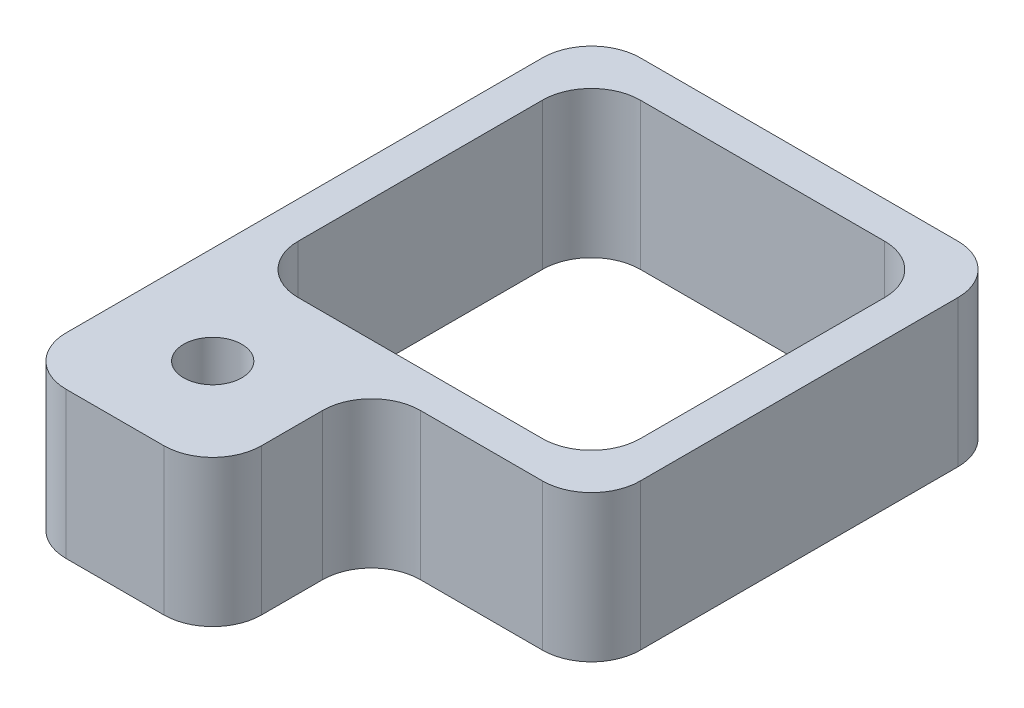
SolidWorks part; units mm, degrees
ref_plane "Front Plane" through (0, 0, 0) normal (0, 0, 1) x (1, 0, 0)
ref_plane "Top Plane" through (0, 0, 0) normal (0, 1, 0) x (1, 0, 0)
ref_plane "Right Plane" through (0, 0, 0) normal (1, 0, 0) x (0, 0, -1)
sketch "Sketch1" plane through (0, 0, 0) normal (0, 1, 0) x (1, 0, 0)
  line L1 (-4.25, -4.25) -> (4.25, -4.25)
  line L2 (-4.25, -4.25) -> (-4.25, 4.25)
  line L3 (-4.25, 4.25) -> (4.25, 4.25)
  line L4 (4.25, -4.25) -> (4.25, 4.25)
  line L5 (-4.25, -4.25) -> (4.25, 4.25) construction
  line L6 (-4.25, 4.25) -> (4.25, -4.25) construction
  point P0 (0, 0)
  dimension "D1" = 8.5
  dimension "D2" = 8.5
extrude "Extrude1" add sketch "Sketch1" along normal blind 3
sketch "Sketch3" plane through (0, 0, 4.25) normal (0, 0, 1) x (1, 0, 0)
  line L0 (-4.25, 0) -> (4.25, 0) construction
  line L1 (-4.25, 3) -> (-0.25, 3)
  line L2 (-4.25, 3) -> (-4.25, 0)
  line L3 (-4.25, 0) -> (-0.25, 0)
  line L4 (-0.25, 3) -> (-0.25, 0)
  dimension "D1" = 4
extrude "Extrude3" add sketch "Sketch3" along normal blind 3.25
sketch "Sketch2" plane through (0, 3, 0) normal (0, 1, 0) x (1, 0, 0)
  line L1 (-3.5, -3.5) -> (3.5, -3.5)
  line L2 (-3.5, -3.5) -> (-3.5, 3.5)
  line L3 (-3.5, 3.5) -> (3.5, 3.5)
  line L4 (3.5, -3.5) -> (3.5, 3.5)
  line L5 (-3.5, -3.5) -> (3.5, 3.5) construction
  line L6 (-3.5, 3.5) -> (3.5, -3.5) construction
  point P0 (0, 0)
  dimension "D1" = 7
  dimension "D2" = 7
extrude "Extrude2" cut sketch "Sketch2" against normal through all
hole_wizard "#0-80 Tapped Hole1" positions "3DSketch2" profile "Sketch6" tap size "#0-80" standard "Ansi Inch" end condition through all
sketch3d "3DSketch2"
  line L0 (-0.25, 3, 7.5) -> (-4.25, 3, 7.5) construction
  line L1 (-0.25, 3, 7.5) -> (-0.25, 3, 4.25) construction
  point P0 (-2.25, 3, 5.5)
  dimension "D1" = 2
  dimension "D2" = 2
sketch "Sketch6" plane through (-2.25, 3, 5.5) normal (1, 0, 0) x (0, 0, 1)
  line L0 (0, 0) -> (0, 3.0001)
  line L1 (0, 3.0001) -> (0.5956, 3.0001)
  line L2 (0.5956, 3.0001) -> (0.5956, 0)
  line L5 (0.5956, 0) -> (0, 0)
  line L11 (0, -6.35) -> (0, 107.95) construction
  dimension "Thread Major Dia." = 1.1913
  dimension "Thru Tap Drill Depth" = 3.0001
sketch "Sketch11" plane through (0, 0, -4.25) normal (0, 0, -1) x (-1, 0, 0)
  line L0 (-4.25, 0) -> (4.25, 0) construction
  line L1 (-1.4296, 1) -> (0.5704, 1)
  line L2 (-1.4296, 1) -> (-1.4296, 0)
  line L3 (-1.4296, 0) -> (0.5704, 0)
  line L4 (0.5704, 1) -> (0.5704, 0)
  line L5 (-1.4296, 1) -> (0.5704, 0) construction
  line L6 (-1.4296, 0) -> (0.5704, 1) construction
  point P0 (-0.4296, 0.5)
  dimension "D1" = 0.5
  dimension "D2" = 2
extrude "Extrude5" add sketch "Sketch11" along normal blind 1.5
fillet "Fillet1" radius 1 10 edges at (3.5, 1.5, -3.5) (-3.5, 1.5, -3.5) (-3.5, 1.5, 3.5) (3.5, 1.5, 3.5) (-4.25, 1.5, 7.5) (-0.25, 1.5, 7.5) (4.25, 1.5, 4.25) (4.25, 1.5, -4.25) (-4.25, 1.5, -4.25)
